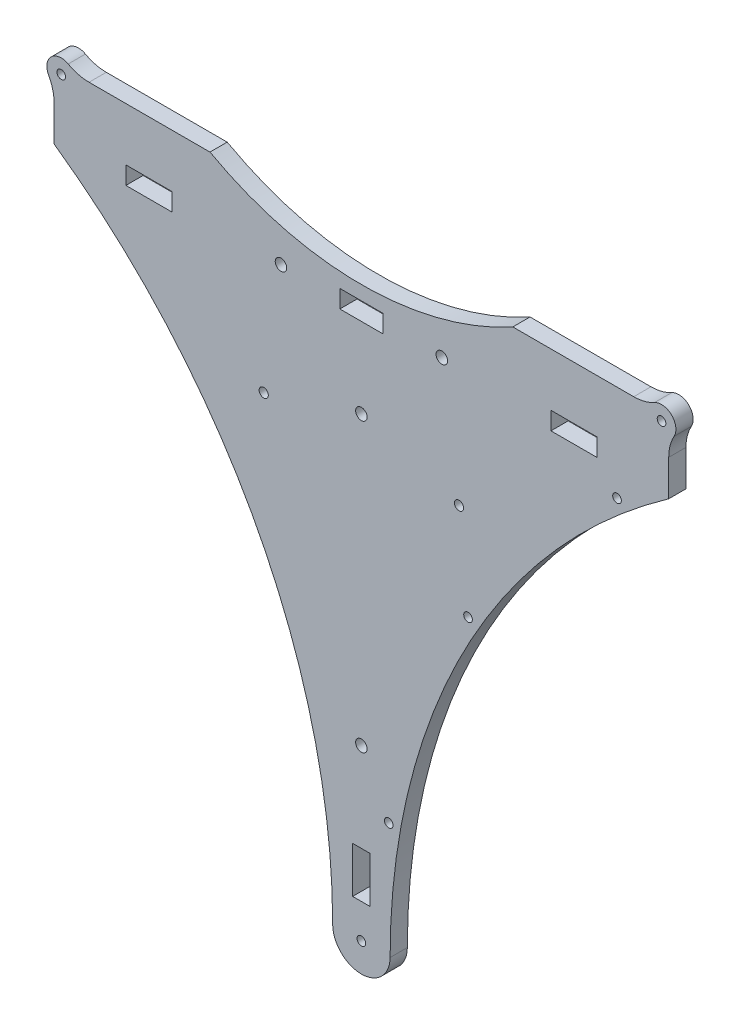
SolidWorks part; units mm, degrees
material "Oak"
ref_plane "Front Plane" through (0, 0, 0) normal (0, 0, 1) x (1, 0, 0)
ref_plane "Top Plane" through (0, 0, 0) normal (0, 1, 0) x (1, 0, 0)
ref_plane "Right Plane" through (0, 0, 0) normal (1, 0, 0) x (0, 0, -1)
sketch "Sketch1" plane through (0, 0, 0) normal (0, 0, 1) x (1, 0, 0)
  line L0 (-66, 82.3) -> (66, 82.3) construction
  line L1 (0, 82.3) -> (0, 0) construction
  line L2 (86.2011, 107) -> (94.8175, 107)
  line L6 (0, -76.6) -> (0, -116.5) construction
  line L7 (-10, -104.5) -> (10, -104.5) construction
  line L8 (-107, 82.3) -> (-107, 94.8175)
  line L9 (-94.8175, 107) -> (-91.7989, 107)
  line L10 (107, 82.3) -> (107, 94.8175)
  line L13 (-82, 88.5) -> (-66, 88.5)
  line L14 (-82, 88.5) -> (-82, 82.3)
  line L15 (-82, 82.3) -> (-66, 82.3)
  line L16 (-66, 88.5) -> (-66, 82.3)
  line L17 (82, 88.5) -> (66, 88.5)
  line L18 (82, 88.5) -> (82, 82.3)
  line L19 (82, 82.3) -> (66, 82.3)
  line L20 (66, 88.5) -> (66, 82.3)
  line L21 (-3.05, -92.6) -> (3.05, -92.6)
  line L22 (-3.05, -92.6) -> (-3.05, -76.6)
  line L23 (-3.05, -76.6) -> (3.05, -76.6)
  line L24 (3.05, -92.6) -> (3.05, -76.6)
  line L32 (52.7171, 107) -> (86.2011, 107)
  line L33 (-7.5, 82.3) -> (7.5, 82.3)
  line L34 (-7.5, 82.3) -> (-7.5, 88.5)
  line L35 (-7.5, 88.5) -> (7.5, 88.5)
  line L36 (7.5, 82.3) -> (7.5, 88.5)
  line L37 (-28, 85.4) -> (28, 85.4) construction
  line L38 (0, 82.3) -> (0, 88.5) construction
  line L40 (-91.7989, 107) -> (-52.7171, 107)
  circle A0 centre (-104.5, 104.5) radius 1.5
  circle A1 centre (104.5, 104.5) radius 1.5
  arc A2 (-52.7171, 107) -> (52.7171, 107) centre (0, 202.3724) ccw
  circle A3 centre (-28, 85.4) radius 2
  circle A4 centre (0, 104.5) radius 1.5 construction
  circle A5 centre (-34, 43.8) radius 1.6
  circle A6 centre (0, 54.4) radius 2
  circle A7 centre (0, -104.5) radius 1.5
  arc A8 (-10, -104.5) -> (10, -104.5) centre (0, -104.5) ccw
  circle A9 centre (0, -45.6) radius 2
  circle A10 centre (28, 85.4) radius 2
  circle A11 centre (-104.5, 0) radius 1.5 [skipped]
  arc A12 (-10, -104.5) -> (-107, 82.3) centre (-238.3672, -104.5) ccw
  arc A13 (10, -104.5) -> (107, 82.3) centre (238.3672, -104.5) cw
  circle A14 centre (104.5, -104.5) radius 1.5 [skipped]
  circle A15 centre (-104.5, -104.5) radius 1.5 [skipped]
  circle A16 centre (104.5, 0) radius 1.5 [skipped]
  arc A17 (108.875, 102.0794) -> (102.0794, 108.875) centre (104.5, 104.5) ccw
  arc A18 (108.875, 102.0794) -> (107, 94.8175) centre (122, 94.8175) ccw
  arc A19 (102.0794, 108.875) -> (94.8175, 107) centre (94.8175, 122) cw
  arc A20 (-102.0794, 108.875) -> (-108.875, 102.0794) centre (-104.5, 104.5) ccw
  arc A21 (-108.875, 102.0794) -> (-107, 94.8175) centre (-122, 94.8175) cw
  arc A22 (-102.0794, 108.875) -> (-94.8175, 107) centre (-94.8175, 122) ccw
  circle A23 centre (34, 43.8) radius 1.6
  point P36 (0, 93.4)
  point P69 (0, 85.4)
  dimension "D4" = 3
  dimension "D10" = 4
  dimension "D19" = 3.2
  dimension "D20" = 15
  dimension "D26" = 5
  dimension "D6" = 6.2
  dimension "D7" = 16
  dimension "D8" = 18.5
  dimension "D15" = 214
  dimension "D21" = 15
  dimension "D22" = 6.1
  dimension "D5" = 209
  dimension "D23" = 28
  dimension "D9" = 181.1
  dimension "D11" = 100
  dimension "D14" = 31
  dimension "D12" = 20
  dimension "D16" = 13.6
  dimension "D17" = 82
  dimension "D24" = 38.5
  dimension "D25" = 34
  dimension "D13" = 4
extrude "Boss-Extrude1" add sketch "Sketch1" along normal blind 6
sketch "Sketch2" plane through (0, 0, 6) normal (0, 0, 1) x (1, 0, 0)
  line L0 (238.3672, -104.5) -> (0, -104.5) construction
  line L1 (238.3672, -104.5) -> (9.5302, -64.1499) construction
  line L2 (238.3672, -104.5) -> (37.1313, 11.6836) construction
  line L3 (238.3672, -104.5) -> (89.0044, 73.5036) construction
  arc A0 (117.5495, 93.9883) -> (6.5512, -120.4956) centre (238.3672, -104.5) ccw construction
  arc A1 (107, 82.3) -> (10, -104.5) centre (238.3672, -104.5) ccw construction
  circle A2 centre (9.5302, -64.1499) radius 1.5
  circle A3 centre (37.1313, 11.6836) radius 1.5
  circle A4 centre (89.0044, 73.5036) radius 1.5
  dimension "D1" = 4
  dimension "D2" = 3
  dimension "D3" = 10
  dimension "D4" = 30
  dimension "D5" = 50
extrude "Cut-Extrude1" cut sketch "Sketch2" against normal through all
equation "\"bed-plate-thickness\"=6"
equation "\"D1@Boss-Extrude1\"=\"bed-plate-thickness\""
equation "\"D22@Sketch1\"=\"y-cross-rib-thickness\"+0.1"
equation "\"D6@Sketch1\"=\"y-rib-thickness\"+0.2"
equation "\"y-cross-rib-thickness\"=6"
equation "\"y-rib-thickness\"=6"
equation "\"x-plate-thickness\"=5"
equation "\"rod-diameter\"=12"
equation "\"t-nut-hole-diameter\"=3"
equation "\"D14@Sketch1\"=28+(\"y-rib-thickness\"/2)"
